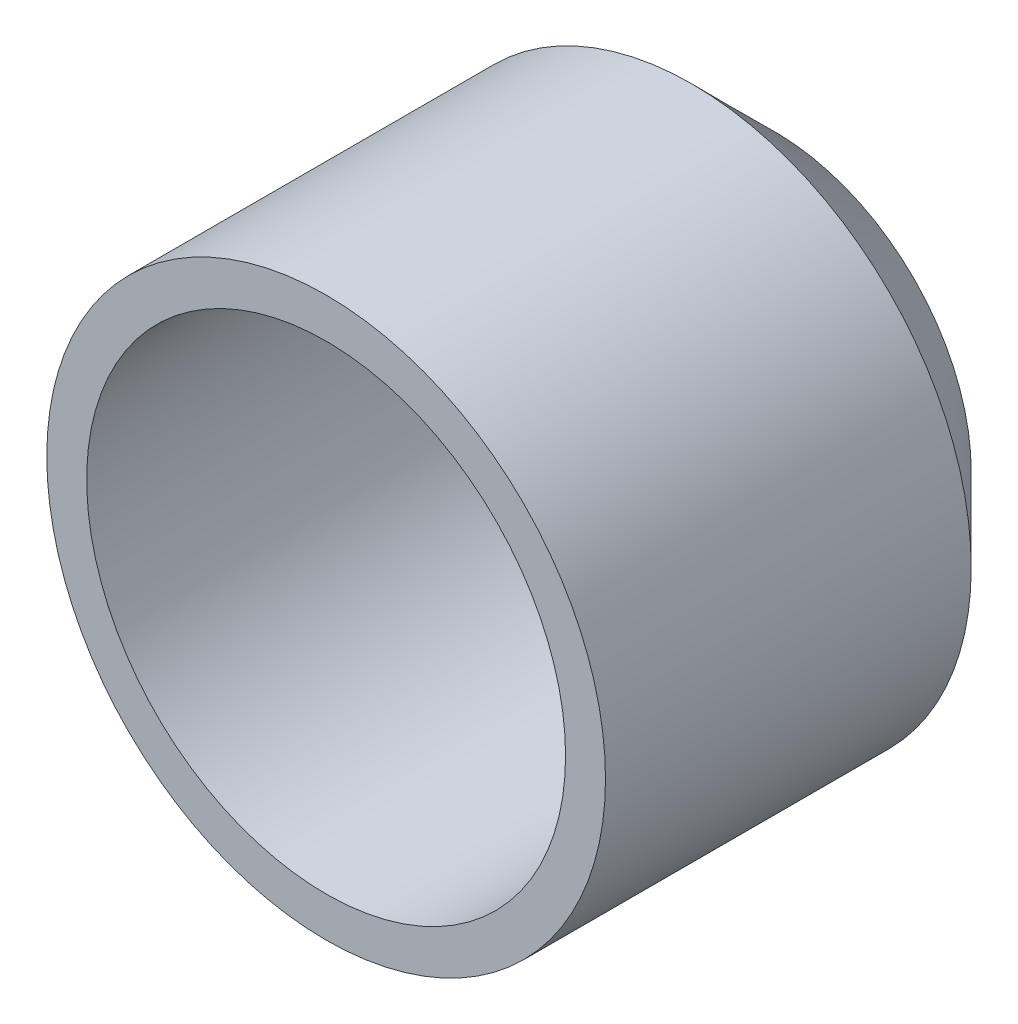
SolidWorks part; units mm, degrees
ref_plane "Front Plane" through (0, 0, 0) normal (0, 0, 1) x (1, 0, 0)
ref_plane "Top Plane" through (0, 0, 0) normal (0, 1, 0) x (1, 0, 0)
ref_plane "Right Plane" through (0, 0, 0) normal (1, 0, 0) x (0, 0, -1)
sketch "Sketch2" plane through (0, 0, 0) normal (1, 0, 0) x (0, 0, -1)
  line L0 (0, 0) -> (0, 19.6569)
  line L1 (0, 19.6569) -> (-8.3431, 28)
  line L2 (-8.3431, 28) -> (-45, 28)
  line L3 (-45, 28) -> (-45, 24)
  line L6 (-4, 0) -> (0, 0)
  line L7 (-45, 24) -> (-10, 24)
  line L8 (-10, 24) -> (-4, 18)
  line L9 (-4, 18) -> (-4, 0)
  dimension "D1" = 4
  dimension "D2" = 4
  dimension "D3" = 24
  dimension "D4" = 45
  dimension "D5" = 45
  dimension "D6" = 4
  dimension "D7" = 35
revolve "Revolve1" add sketch "Sketch2" angle 360 about L6
